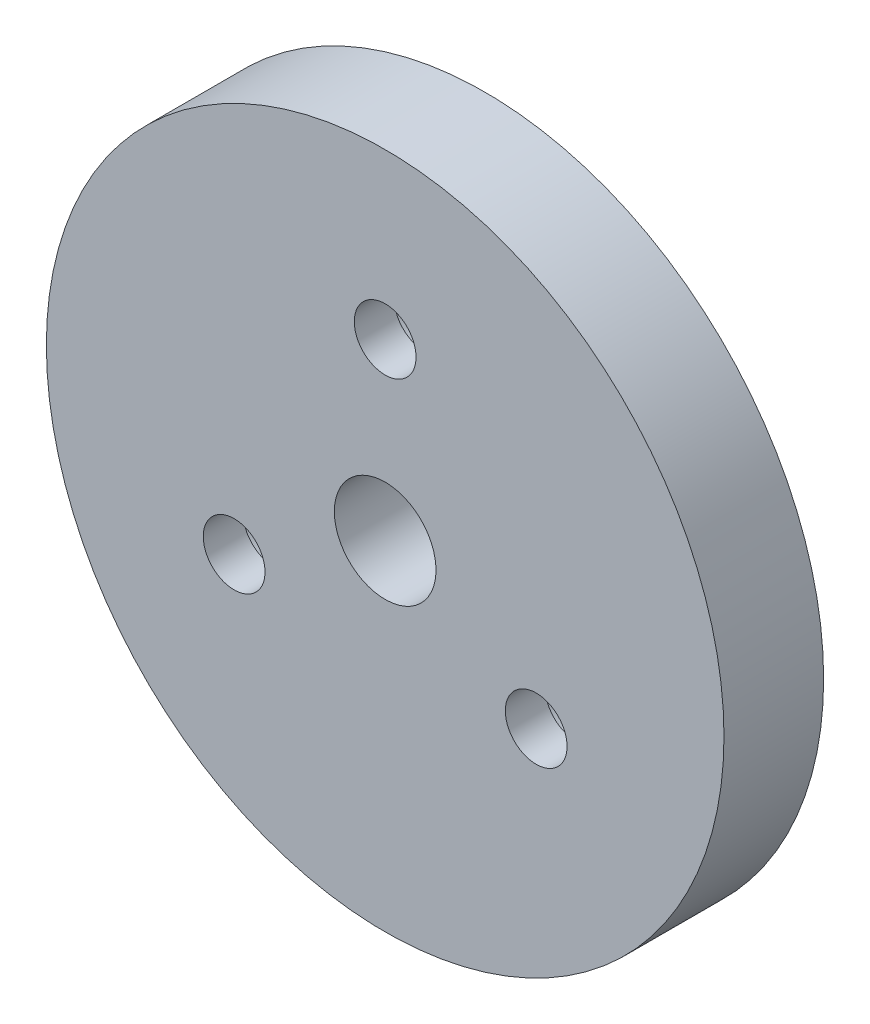
SolidWorks part; units mm, degrees
material "Thornel Mat VMA"
ref_plane "前视基准面" through (0, 0, 0) normal (0, 0, 1) x (1, 0, 0)
ref_plane "上视基准面" through (0, 0, 0) normal (0, 1, 0) x (1, 0, 0)
ref_plane "右视基准面" through (0, 0, 0) normal (1, 0, 0) x (0, 0, -1)
sketch "草图1" plane through (0, 0, 0) normal (0, 0, 1) x (1, 0, 0)
  circle A0 centre (0, 0) radius 17
extrude "凸台-拉伸1" add sketch "草图1" along normal blind 5
sketch "草图2" plane through (0, 0, 0) normal (0, 0, -1) x (-1, 0, 0)
  line L0 (0, 8.75) -> (0, 0) construction
  line L1 (0, 0) -> (7.5777, -4.375) construction
  line L2 (0, 0) -> (-7.5777, -4.375) construction
  circle A0 centre (0, 0) radius 8.75 construction
  circle A2 centre (0, 8.75) radius 2.8
  circle A3 centre (7.5777, -4.375) radius 2.8
  circle A4 centre (-7.5777, -4.375) radius 2.8
  dimension "D1" = 120
  dimension "D2" = 120
extrude "切除-拉伸1" cut sketch "草图2" against normal blind 3
sketch "草图3" plane through (0, 0, 0) normal (0, 0, -1) x (-1, 0, 0)
  circle A0 centre (0, 0) radius 2.55
extrude "切除-拉伸2" cut sketch "草图3" against normal through all
sketch "草图7" plane through (0, 0, 3) normal (0, 0, -1) x (-1, 0, 0)
  line L0 (0, 0) -> (0, 8.75) construction
  line L1 (0, 0) -> (7.5777, -4.375) construction
  line L2 (0, 0) -> (-7.5777, -4.375) construction
  circle A0 centre (0, 0) radius 8.75 construction
  circle A1 centre (-7.5777, -4.375) radius 1.55
  circle A2 centre (7.5777, -4.375) radius 1.55
  circle A3 centre (0, 8.75) radius 1.55
  dimension "D1" = 120
  dimension "D2" = 120
extrude "切除-拉伸4" cut sketch "草图7" against normal through all
